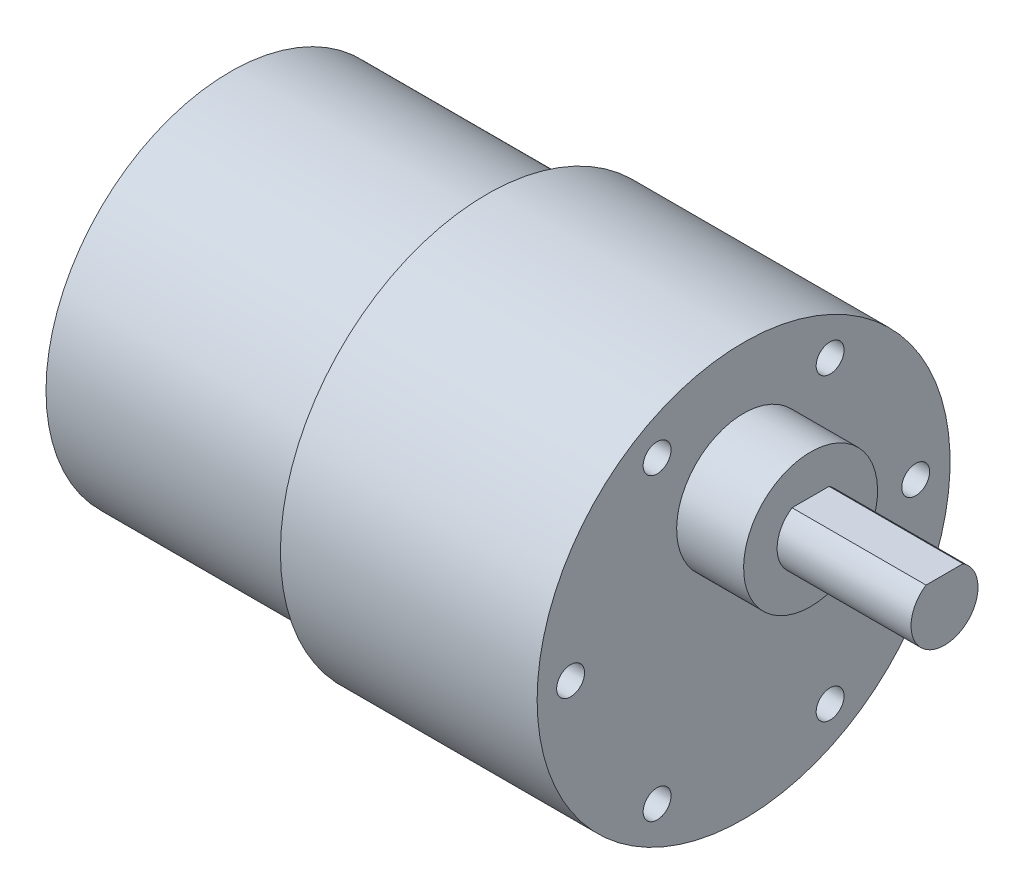
SolidWorks part; units mm, degrees
ref_plane "前视基准面" through (0, 0, 0) normal (0, 0, 1) x (1, 0, 0)
ref_plane "上视基准面" through (0, 0, 0) normal (0, 1, 0) x (1, 0, 0)
ref_plane "右视基准面" through (0, 0, 0) normal (1, 0, 0) x (0, 0, -1)
sketch "草图1" plane through (0, 0, 0) normal (0, 0, 1) x (1, 0, 0)
  line L0 (0, 0) -> (46, 0)
  line L1 (46, 0) -> (46, 18.5)
  line L2 (46, 18.5) -> (23, 18.5)
  line L3 (23, 18.5) -> (23, 16.5)
  line L4 (23, 16.5) -> (0, 16.5)
  line L5 (0, 16.5) -> (0, 0)
  dimension "D1" = 16.5
  dimension "D2" = 18.5
  dimension "D3" = 23
  dimension "D4" = 23
revolve "旋转1" add sketch "草图1" angle 360 about L0
sketch "草图2" plane through (0, 0, 0) normal (0, 0, 1) x (1, 0, 0)
  line L0 (46, 7) -> (64, 7)
  line L1 (46, -18.5) -> (46, 18.5) construction
  line L2 (64, 7) -> (64, 4)
  line L3 (64, 4) -> (52, 4)
  line L4 (52, 4) -> (52, 1)
  line L5 (52, 1) -> (46, 1)
  line L6 (46, 1) -> (46, 7)
  point P4 (46, 9.9221)
  dimension "D1" = 6
  dimension "D2" = 12
  dimension "D3" = 3
  dimension "D4" = 6
  dimension "D5" = 7
revolve "旋转2" add sketch "草图2" angle 360 about L0
sketch "草图3" plane through (64, 0, 0) normal (1, 0, 0) x (0, 0, -1)
  line L1 (-6.1988, 10.4536) -> (5.4544, 10.4536)
  line L2 (-6.1988, 10.4536) -> (-6.1988, 9.5)
  line L3 (-6.1988, 9.5) -> (5.4544, 9.5)
  line L4 (5.4544, 10.4536) -> (5.4544, 9.5)
  line L5 (-6.1988, 10.4536) -> (5.4544, 9.5) construction
  line L6 (-6.1988, 9.5) -> (5.4544, 10.4536) construction
  circle A0 centre (0, 7) radius 3 construction
  circle A1 centre (0, 7) radius 3 construction
  circle A2 centre (0, 7) radius 6 construction
  point P0 (-0.3722, 9.9768)
  dimension "D1" = 11.6531
  dimension "D2" = 2.5
extrude "切除-拉伸1" cut sketch "草图3" against normal up to surface (12 mm away) up to face at (52, 4, 0)
sketch "草图4" plane through (46, 0, 0) normal (1, 0, 0) x (0, 0, -1)
  line L1 (15.5, 0) -> (7.75, 13.4234)
  line L2 (7.75, 13.4234) -> (-7.75, 13.4234)
  line L3 (-7.75, 13.4234) -> (-15.5, 0)
  line L4 (-15.5, 0) -> (-7.75, -13.4234)
  line L5 (-7.75, -13.4234) -> (7.75, -13.4234)
  line L6 (7.75, -13.4234) -> (15.5, 0)
  circle A0 centre (0, 0) radius 15.5 construction
  dimension "D1" = 31
hole_wizard "M3 螺纹孔1" positions "草图5" profile "草图7" tap size "M3" standard "ISO"
sketch "草图5" plane through (46, 0, 0) normal (1, 0, 0) x (0, 0, -1)
  line L0 (15.5, 0) -> (7.75, 13.4234) construction
  point P0 (-7.75, 13.4234)
  point P4 (7.75, 13.4234)
  point P7 (15.4165, 0.1446)
  point P11 (7.75, -13.4234)
  point P14 (-7.75, -13.4234)
  point P17 (-15.5, 0)
sketch "草图7" plane through (46, 13.4234, 7.75) normal (0, 1, 0) x (0, 0, -1)
  line L0 (0, 0) -> (0, 8.2511)
  line L1 (0, 8.2511) -> (1.25, 7.5)
  line L2 (1.25, 7.5) -> (1.25, 0)
  line L5 (1.25, 0) -> (0, 0)
  line L10 (0, 8.2511) -> (-1.25, 7.5) construction
  line L11 (0, -6.35) -> (0, 107.95) construction
  dimension "螺纹孔钻头直径" = 2.5
  dimension "螺纹孔钻头深度" = 7.5
  dimension "导头角度" = 118
cosmetic thread "孔螺蚊线1" parameters "D1"=6, "D2"=3
cosmetic thread "孔螺蚊线2" parameters "D1"=6, "D2"=3
cosmetic thread "孔螺蚊线3" parameters "D1"=6, "D2"=3
cosmetic thread "孔螺蚊线4" parameters "D1"=6, "D2"=3
cosmetic thread "孔螺蚊线5" parameters "D1"=6, "D2"=3
cosmetic thread "孔螺蚊线6" parameters "D1"=6, "D2"=3
